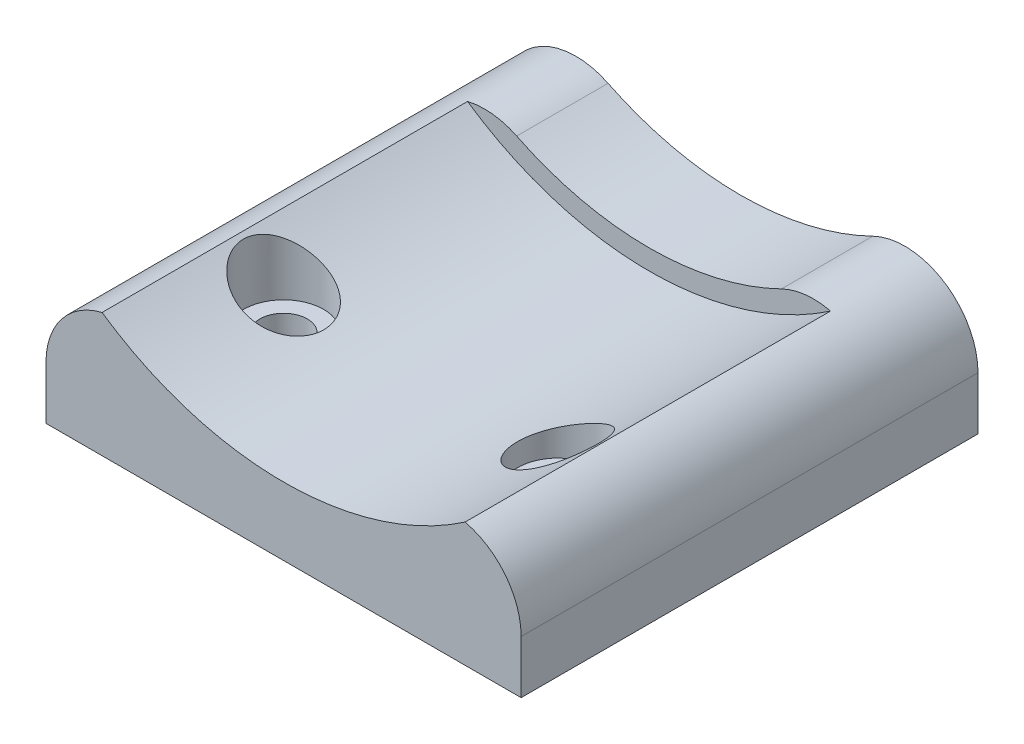
SolidWorks part; units mm, degrees
ref_plane "Front Plane" through (0, 0, 0) normal (0, 0, 1) x (1, 0, 0)
ref_plane "Top Plane" through (0, 0, 0) normal (0, 1, 0) x (1, 0, 0)
ref_plane "Right Plane" through (0, 0, 0) normal (1, 0, 0) x (0, 0, -1)
sketch "Sketch2" plane through (0, 0, 0) normal (0, 0, 1) x (1, 0, 0)
  line L0 (-33.02, 0) -> (-33.02, 7.366)
  line L2 (33.02, 7.366) -> (33.02, 0)
  line L3 (33.02, 0) -> (-33.02, 0)
  arc A6 (-18.3995, 16.4945) -> (18.3995, 16.4945) centre (0, 54.1496) ccw
  arc A7 (18.3995, 16.4945) -> (33.02, 7.366) centre (22.86, 7.366) cw
  arc A8 (-33.02, 7.366) -> (-18.3995, 16.4945) centre (-22.86, 7.366) cw
  point P9 (0, 0)
  dimension "D1" = 10.16
  dimension "D3" = 41.91
  dimension "D5" = 66.04
  dimension "D4" = 7.366
  dimension "D6" = 7.366
extrude "Boss-Extrude1" add sketch "Sketch2" against normal blind 63.5
sketch "Sketch7" plane through (0, 0, 0) normal (0, 0, 1) x (1, 0, 0)
  circle A0 centre (0, 54.1496) radius 44.704
  arc A1 (-18.3995, 16.4945) -> (18.3995, 16.4945) centre (0, 54.1496) ccw construction
  dimension "D1" = 89.408
  dimension "D2" = 0
extrude "Cut-Extrude1" cut sketch "Sketch7" against normal blind 50.8
sketch "Sketch8" plane through (0, 0, 0) normal (0, -1, 0) x (-1, 0, 0)
  line L2 (-25.23, 0) -> (25.23, 0) construction
  line L3 (19.05, 19.05) -> (-19.05, 19.05) construction
  circle A0 centre (19.05, 19.05) radius 3.302
  circle A1 centre (-19.05, 19.05) radius 3.302
  point P4 (0, 19.05)
  dimension "D2" = 6.604
  dimension "D3" = 6.604
  dimension "D1" = 38.1
  dimension "D5" = 19.05
  dimension "D6" = 19.05
extrude "Cut-Extrude2" cut sketch "Sketch8" against normal through all
ref_plane "Plane1" through (0, 8.382, 0) normal (0, -1, 0) x (-1, 0, 0)
sketch "Sketch9" plane through (0, 8.382, 0) normal (0, -1, 0) x (-1, 0, 0)
  circle A0 centre (19.05, 19.05) radius 5.588
  circle A1 centre (-19.05, 19.05) radius 5.588
  dimension "D1" = 11.176
  dimension "D2" = 11.176
extrude "Cut-Extrude3" cut sketch "Sketch9" against normal through all
